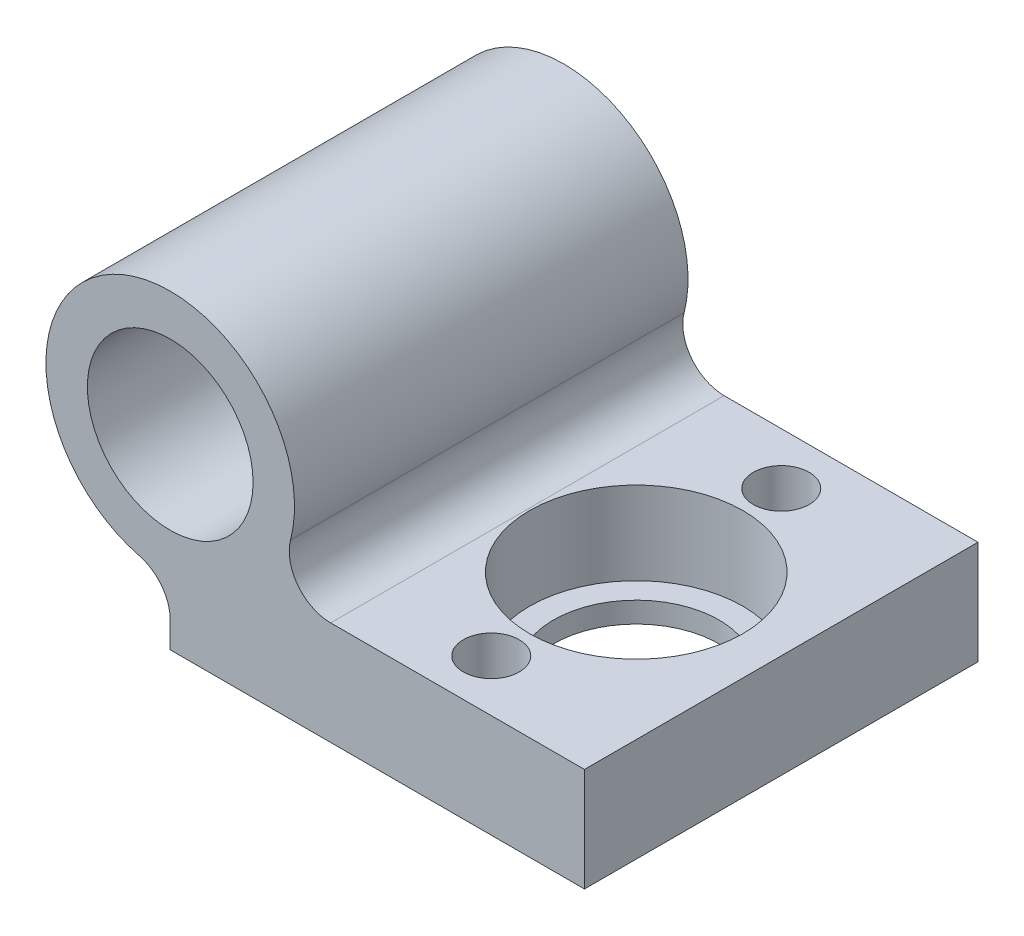
SolidWorks part; units mm, degrees
ref_plane "Front Plane" through (0, 0, 0) normal (0, 0, 1) x (1, 0, 0)
ref_plane "Top Plane" through (0, 0, 0) normal (0, 1, 0) x (1, 0, 0)
ref_plane "Right Plane" through (0, 0, 0) normal (1, 0, 0) x (0, 0, -1)
sketch "Sketch1" plane through (0, 0, 0) normal (0, 0, 1) x (1, 0, 0)
  circle A0 centre (0, 0) radius 4
  circle A1 centre (0, 0) radius 6
  dimension "D1" = 12
  dimension "D2" = 8
extrude "Main" add sketch "Sketch1" along normal mid plane 19
ref_plane "Plane1" through (0, -9, 0) normal (0, 1, 0) x (1, 0, 0)
sketch "Sketch2" plane through (0, -9, 0) normal (0, 1, 0) x (1, 0, 0)
  line L0 (6, 9.5) -> (-6, 9.5) construction
  line L1 (0, 9.5) -> (20, 9.5)
  line L2 (0, 9.5) -> (0, -9.5)
  line L3 (0, -9.5) -> (20, -9.5)
  line L4 (20, 9.5) -> (20, -9.5)
  line L5 (-6, -9.5) -> (6, -9.5) construction
  line L7 (13, 7) -> (13, -7) construction
  circle A0 centre (13, 0) radius 4
  circle A1 centre (13, 7) radius 1.35
  circle A2 centre (13, -7) radius 1.35
  dimension "D4" = 8
  dimension "D5" = 2.7
  dimension "D2" = 20
  dimension "D3" = 7
  dimension "D6" = 14
extrude "BallSupportExtrusion" add sketch "Sketch2" along normal blind 5
sketch "Sketch3" plane through (0, -4, 0) normal (0, 1, 0) x (1, 0, 0)
  circle A0 centre (13, 0) radius 5.15
  dimension "D1" = 10.3
extrude "BallSupportHole" cut sketch "Sketch3" against normal blind 4
fillet "Fillet2" radius 2 2 edges at (4.4721, -4, 0) (0, -6, 0)
